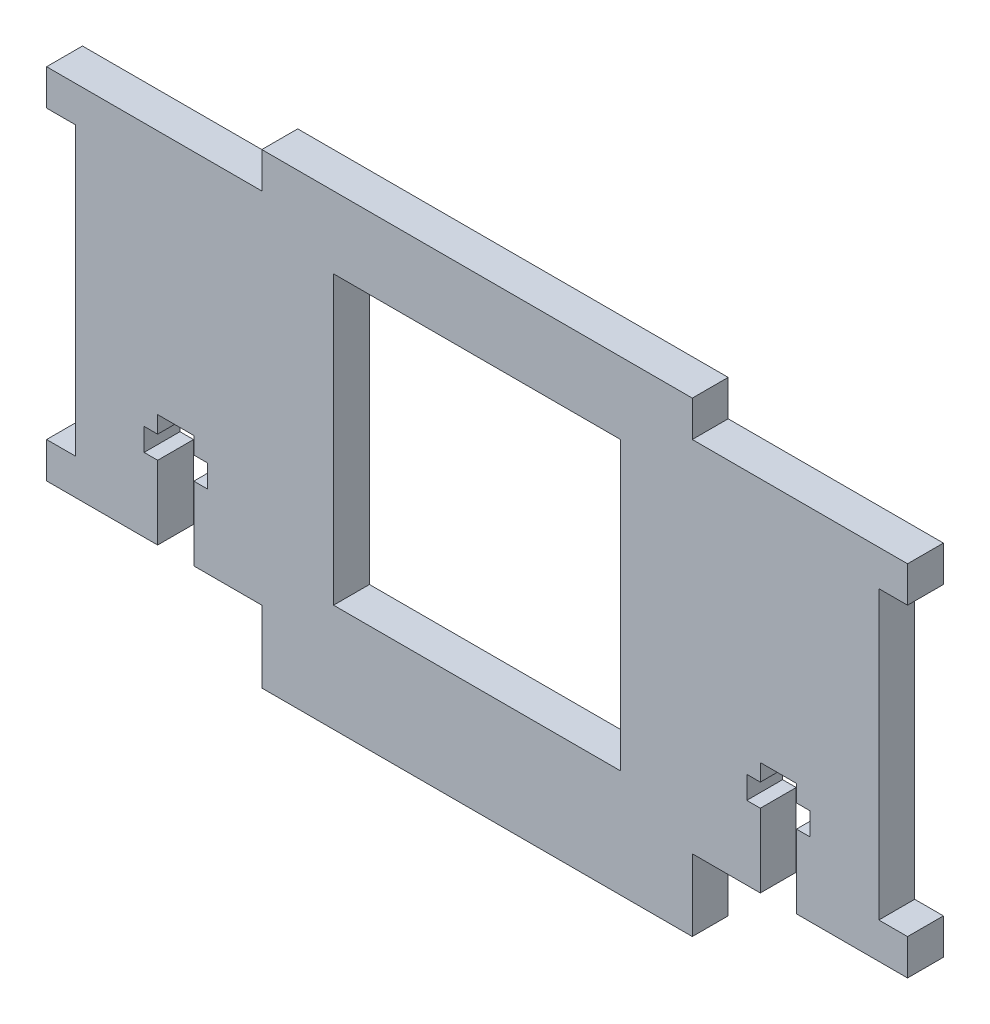
SolidWorks part; units mm, degrees
ref_plane "Front Plane" through (0, 0, 0) normal (0, 0, 1) x (1, 0, 0)
ref_plane "Top Plane" through (0, 0, 0) normal (0, 1, 0) x (1, 0, 0)
ref_plane "Right Plane" through (0, 0, 0) normal (1, 0, 0) x (0, 0, -1)
sketch "Sketch1" plane through (0, 0, 0) normal (0, 0, 1) x (1, 0, 0)
  line L0 (19.05, 33.3375) -> (0, 33.3375) construction
  line L1 (0, 0) -> (19.05, 0)
  line L2 (0, 0) -> (0, 3.175)
  line L3 (0, 31.75) -> (19.05, 31.75)
  line L4 (76.2, 0) -> (76.2, 3.175)
  line L6 (19.05, 0) -> (19.05, -6.35)
  line L7 (19.05, -6.35) -> (57.15, -6.35)
  line L8 (57.15, 0) -> (57.15, -6.35)
  line L9 (76.2, 28.575) -> (76.2, 31.75)
  line L10 (19.05, 31.75) -> (19.05, 34.925)
  line L11 (19.05, 34.925) -> (57.15, 34.925)
  line L12 (57.15, 31.75) -> (57.15, 34.925)
  line L13 (57.15, 33.3375) -> (76.2, 33.3375) construction
  line L14 (57.15, -3.175) -> (76.2, -3.175) construction
  line L15 (19.05, -3.175) -> (0, -3.175) construction
  line L16 (1.27, 3.175) -> (1.27, 0) construction
  line L17 (0, 28.575) -> (2.54, 28.575)
  line L18 (57.15, 31.75) -> (76.2, 31.75)
  line L19 (0, 3.175) -> (2.54, 3.175)
  line L20 (2.54, 28.575) -> (2.54, 3.175)
  line L21 (76.2, 28.575) -> (73.66, 28.575)
  line L22 (57.15, 0) -> (76.2, 0)
  line L23 (76.2, 3.175) -> (73.66, 3.175)
  line L24 (73.66, 28.575) -> (73.66, 3.175)
  line L25 (25.4, 3.175) -> (50.8, 3.175)
  line L26 (25.4, 3.175) -> (25.4, 28.575)
  line L27 (25.4, 28.575) -> (50.8, 28.575)
  line L28 (50.8, 3.175) -> (50.8, 28.575)
  line L29 (1.27, 28.575) -> (1.27, 31.75) construction
  line L30 (38.1, 34.925) -> (38.1, 28.575) construction
  line L31 (38.1, 28.575) -> (38.1, 3.175) construction
  line L32 (38.1, 3.175) -> (38.1, -6.35) construction
  line L33 (0, 28.575) -> (0, 31.75)
  dimension "D1" = 6.35
  dimension "D2" = 3.175
  dimension "D3" = 38.1
  dimension "D4" = 76.2
  dimension "D5" = 31.75
  dimension "D6" = 25.4
  dimension "D7" = 2.54
  dimension "D8" = 25.4
extrude "Boss-Extrude1" add sketch "Sketch1" along normal blind 3.175
sketch "Sketch2" plane through (0, 0, 3.175) normal (0, 0, 1) x (1, 0, 0)
  line L0 (0, 0) -> (19.05, 0) construction
  line L1 (13.03, 0) -> (9.83, 0)
  line L2 (13.03, 0) -> (13.03, 6.5)
  line L3 (13.03, 10) -> (9.83, 10)
  line L4 (9.83, 0) -> (9.83, 6.5)
  line L5 (19.05, -3.175) -> (11.43, -3.175) construction
  line L6 (19.05, 0) -> (19.05, -6.35) construction
  line L7 (11.43, -3.175) -> (11.43, 0) construction
  line L8 (8.63, 7.5) -> (14.23, 7.5) construction
  line L9 (9.83, 8.5) -> (8.63, 8.5)
  line L10 (13.03, 8.5) -> (13.03, 10)
  line L11 (9.83, 6.5) -> (8.63, 6.5)
  line L12 (8.63, 8.5) -> (8.63, 6.5)
  line L13 (13.03, 8.5) -> (14.23, 8.5)
  line L14 (38.1, 34.925) -> (38.1, -6.35) construction
  line L15 (13.03, 6.5) -> (14.23, 6.5)
  line L16 (14.23, 8.5) -> (14.23, 6.5)
  line L17 (9.83, 8.5) -> (9.83, 10)
  line L18 (57.15, 34.925) -> (19.05, 34.925) construction
  line L19 (19.05, -6.35) -> (57.15, -6.35) construction
  line L20 (2.54, 15.875) -> (73.66, 15.875) construction
  line L22 (2.54, 28.575) -> (2.54, 3.175) construction
  line L23 (73.66, 3.175) -> (73.66, 28.575) construction
  line L24 (67.57, 7.5) -> (61.97, 7.5) construction
  line L25 (66.37, 8.5) -> (66.37, 10)
  line L26 (61.97, 8.5) -> (61.97, 6.5)
  line L27 (63.17, 6.5) -> (61.97, 6.5)
  line L28 (63.17, 8.5) -> (61.97, 8.5)
  line L29 (67.57, 8.5) -> (67.57, 6.5)
  line L30 (66.37, 6.5) -> (67.57, 6.5)
  line L31 (63.17, 8.5) -> (63.17, 10)
  line L32 (66.37, 8.5) -> (67.57, 8.5)
  line L33 (66.37, 0) -> (66.37, 6.5)
  line L34 (63.17, 10) -> (66.37, 10)
  line L35 (63.17, 0) -> (63.17, 6.5)
  line L36 (63.17, 0) -> (66.37, 0)
  line L37 (8.63, 7.5) -> (14.23, 7.5) construction
  dimension "D1" = 7.62
  dimension "D2" = 10
  dimension "D3" = 3.2
  dimension "D4" = 7.5
  dimension "D5" = 5.6
  dimension "D6" = 2
extrude "Cut-Extrude1" cut sketch "Sketch2" against normal through all
